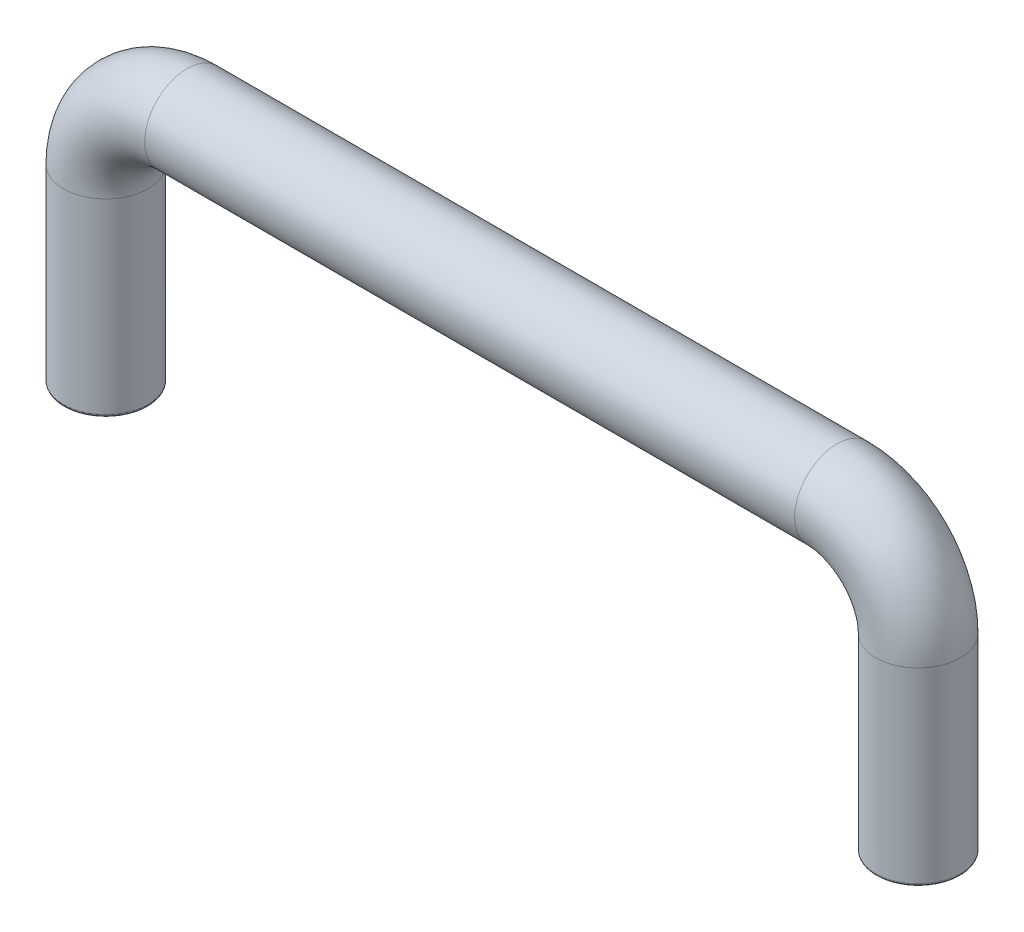
SolidWorks part; units mm, degrees
ref_plane "Front Plane" through (0, 0, 0) normal (0, 0, 1) x (1, 0, 0)
ref_plane "Top Plane" through (0, 0, 0) normal (0, 1, 0) x (1, 0, 0)
ref_plane "Right Plane" through (0, 0, 0) normal (1, 0, 0) x (0, 0, -1)
sketch "Sketch1" plane through (0, 0, 0) normal (0, 0, 1) x (1, 0, 0)
  line L0 (0, 0) -> (0, 17.78)
  line L1 (7.62, 25.4) -> (68.58, 25.4)
  line L2 (76.2, 17.78) -> (76.2, 0)
  arc A0 (68.58, 25.4) -> (76.2, 17.78) centre (68.58, 17.78) cw
  arc A1 (0, 17.78) -> (7.62, 25.4) centre (7.62, 17.78) cw
  point P7 (76.2, 25.4)
  point P10 (0, 25.4)
  dimension "D3" = 7.62
  dimension "D1" = 25.4
  dimension "D2" = 76.2
sketch "Sketch2" plane through (0, 0, 0) normal (0, 1, 0) x (1, 0, 0)
  line L0 (7.62, 0) -> (68.58, 0) construction
  circle A0 centre (76.2, 0) radius 3.9688
  dimension "D1" = 7.9375
  dimension "D2" = 76.2
sweep "Sweep5" add profiles "Sketch2" path "Sketch1"
hole_wizard "Tap Drill for #8-32 Tap1" positions "Sketch3" profile "Sketch5" hole size "#8-32" standard "ANSI Inch"
sketch "Sketch3" plane through (0, 0, 0) normal (0, -1, 0) x (-1, 0, 0)
  point P0 (-76.2, 0)
  point P3 (0, 0)
sketch "Sketch5" plane through (76.2, 0, 0) normal (1, 0, 0) x (0, 0, -1)
  line L0 (0, 0) -> (0, 9.0071)
  line L1 (0, 9.0071) -> (1.7272, 7.9692)
  line L2 (1.7272, 7.9692) -> (1.7272, 0)
  line L5 (1.7272, 0) -> (0, 0)
  line L10 (0, 9.0071) -> (-1.7272, 7.9692) construction
  line L11 (0, -6.35) -> (0, 107.95) construction
  dimension "Hole Dia." = 3.4544
  dimension "Hole Depth" = 7.9692
  dimension "Drill Angle" = 118
fillet "Fillet1" radius 0.254 4 edges at (76.2, 0, 3.9688) (0, 0, 3.9688) (0, 0, -1.7272) (76.2, 0, -1.7272)
